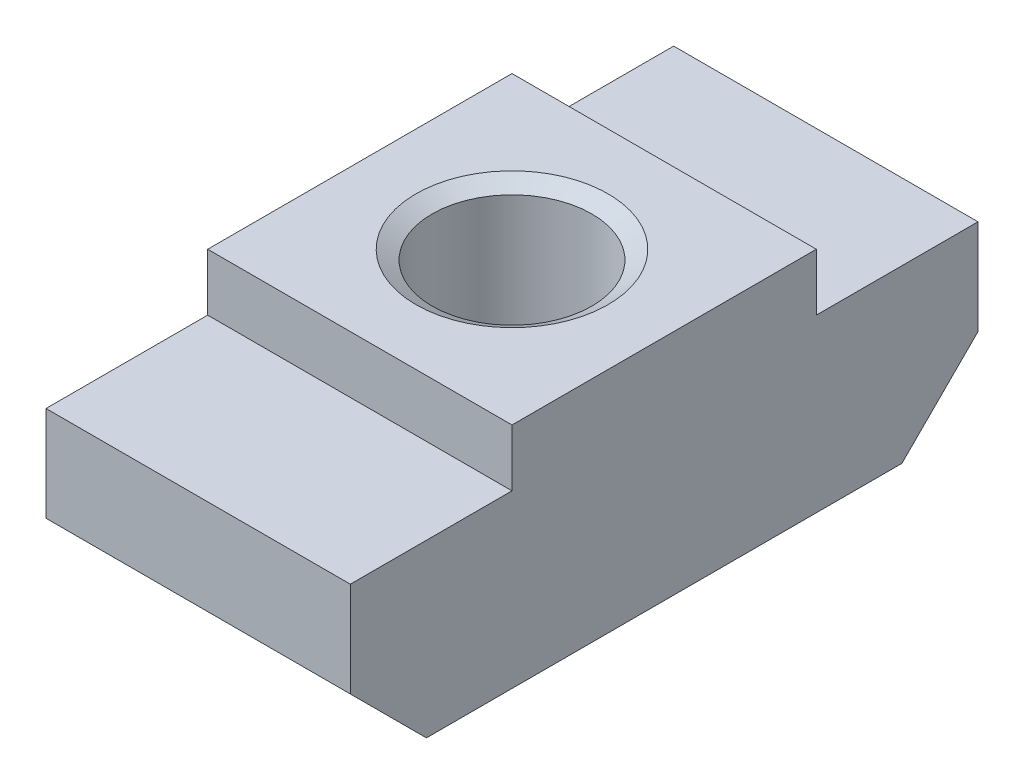
SolidWorks part; units mm, degrees
material "Acciaio al carbonio semplice"
ref_plane "Piano frontale" through (0, 0, 0) normal (0, 0, 1) x (1, 0, 0)
ref_plane "Piano superiore" through (0, 0, 0) normal (0, 1, 0) x (1, 0, 0)
ref_plane "Piano destro" through (0, 0, 0) normal (1, 0, 0) x (0, 0, -1)
sketch "Schizzo1" plane through (0, 0, 0) normal (0, 0, 1) x (1, 0, 0)
  line L0 (-4, 0) -> (4, 0)
  line L1 (-4, 6) -> (-4, 0)
  line L3 (4, 6) -> (4, 0)
  line L5 (-4, 6) -> (4, 6)
  line L6 (0, -16.3778) -> (0, 28.5715) construction
  point P11 (0, 0)
  point P15 (0, 6)
  dimension "D1" = 8
  dimension "D2" = 6
extrude "Estrusione-Estrusione1" add sketch "Schizzo1" along normal blind 16.5
ref_point "Punto1"
hole_wizard "Foro filettato M5-1" positions "Schizzo3" profile "Schizzo2" tap size "M5" standard "ISO" end condition through all
sketch "Schizzo3" plane through (0, 6, 0) normal (0, 1, 0) x (1, 0, 0)
  point P0 (0, -8.25)
sketch "Schizzo2" plane through (0, 6, 8.25) normal (1, 0, 0) x (0, 0, 1)
  line L0 (0, 0) -> (0, 6)
  line L1 (0, 6) -> (2.1, 6)
  line L2 (2.1, 6) -> (2.1, 0.2454)
  line L3 (2.1, 0.2454) -> (2.525, 0)
  line L5 (2.525, 0) -> (0, 0)
  line L6 (-2.1, 0.2454) -> (-2.525, 0) construction
  line L11 (0, -6.35) -> (0, 107.95) construction
  dimension "Thru Tap Drill Dia." = 4.2
  dimension "Thru Tap Drill Depth" = 6
  dimension "Near C'Sink Dia." = 5.05
  dimension "Near C'Sink Angle" = 120
cosmetic thread "Filettatura del foro1" parameters "D2"=5
sketch "Schizzo4" plane through (4, 0, 0) normal (1, 0, 0) x (0, 0, -1)
  line L0 (-16.5, 0) -> (-16.5, 2)
  line L1 (-16.5, 2) -> (-14.5, 0)
  line L2 (-14.5, 0) -> (-16.5, 0)
  line L3 (0, 0) -> (0, 2)
  line L4 (0, 2) -> (-2, 0)
  line L5 (-2, 0) -> (0, 0)
  line L6 (0, 4.5) -> (-4.25, 4.5)
  line L7 (-4.25, 4.5) -> (-4.25, 6)
  line L8 (-4.25, 6) -> (0, 6)
  line L9 (0, 6) -> (0, 4.5)
  line L10 (-16.5, 4.5) -> (-12.25, 4.5)
  line L11 (-12.25, 4.5) -> (-12.25, 6)
  line L12 (-12.25, 6) -> (-16.5, 6)
  line L13 (-16.5, 6) -> (-16.5, 4.5)
  line L14 (-8.25, 7.1074) -> (-8.25, -0.4799) construction
  line L15 (-16.5, 6) -> (0, 6) construction
  line L16 (0, 0) -> (0, 6) construction
  line L17 (-16.5, 0) -> (-16.5, 6) construction
  line L18 (-16.5, 0) -> (0, 0) construction
  dimension "D1" = 1.5
  dimension "D2" = 2
  dimension "D3" = 8
extrude "Taglio-Estrusione1" cut sketch "Schizzo4" against normal blind 10
